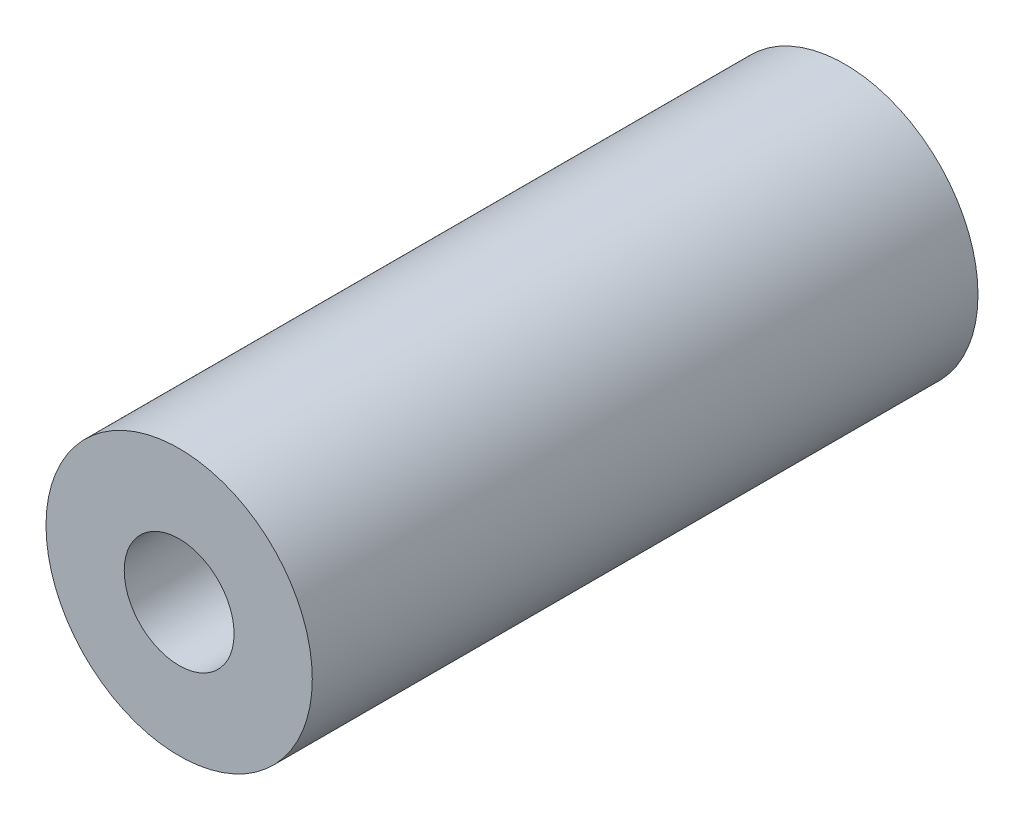
SolidWorks part; units mm, degrees
ref_plane "正面" through (0, 0, 0) normal (0, 0, 1) x (1, 0, 0)
ref_plane "平面" through (0, 0, 0) normal (0, 1, 0) x (1, 0, 0)
ref_plane "右側面" through (0, 0, 0) normal (1, 0, 0) x (0, 0, -1)
sketch "ｽｹｯﾁ1" plane through (0, 0, 0) normal (0, 0, 1) x (1, 0, 0)
  circle A0 centre (0, 0) radius 4
  circle A1 centre (0, 0) radius 1.25
  dimension "D1" = 2.5
  dimension "D2" = 8
extrude "ﾎﾞｽ - 押し出し1" add sketch "ｽｹｯﾁ1" along normal mid plane 20 contours A0 A1 | A1
hole_wizard "M4x0.7 ねじ穴1" positions "3Dｽｹｯﾁ2" profile "ｽｹｯﾁ3" tap size "M4x0.7" standard "JIS"
sketch3d "3Dｽｹｯﾁ2"
  line L0 (0, 0, 10) -> (0, 0, -10) construction
  point P0 (0, 0, 0)
  point P3 (-15.6503, 3.3995, 0)
  point P5 (-15.6503, 3.3995, 0)
  point P7 (-13.6621, 2.5908, 0)
  point P9 (0, 0, 10)
  point P13 (0, 0, 0)
  point P15 (0, 0, 0)
  point P17 (0, 0, -10)
sketch "ｽｹｯﾁ3" plane through (0, 0, -10) normal (1, 0, 0) x (0, 1, 0)
  line L0 (0, 0) -> (0, 12.4914)
  line L1 (0, 12.4914) -> (1.65, 11.5)
  line L2 (1.65, 11.5) -> (1.65, 0)
  line L5 (1.65, 0) -> (0, 0)
  line L10 (0, 12.4914) -> (-1.65, 11.5) construction
  line L11 (0, -6.35) -> (0, 107.95) construction
  dimension "ねじ下穴ﾄﾞﾘﾙ直径" = 3.3
  dimension "ねじ下穴ﾄﾞﾘﾙの深さ" = 11.5
  dimension "ﾄﾞﾘﾙ角度" = 118
cosmetic thread "穴のねじ山7" parameters "D1"=8, "D2"=4
cosmetic thread "穴のねじ山8" parameters "D1"=8, "D2"=4
cosmetic thread "穴のねじ山15" parameters "D1"=8, "D2"=4
cosmetic thread "穴のねじ山16" parameters "D1"=8, "D2"=4
cosmetic thread "穴のねじ山17" parameters "D1"=8, "D2"=4
cosmetic thread "穴のねじ山18" parameters "D1"=8, "D2"=4
cosmetic thread "穴のねじ山19" parameters "D1"=8, "D2"=4
cosmetic thread "穴のねじ山20" parameters "D1"=8, "D2"=4
